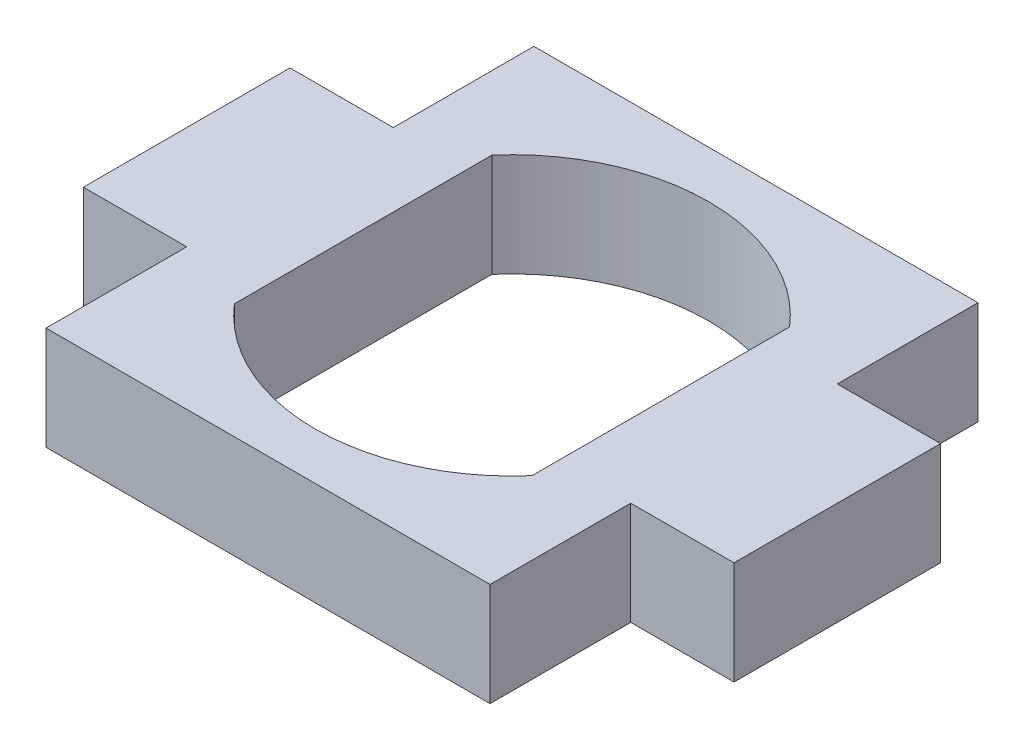
SolidWorks part; units mm, degrees
material "Acrylic (Medium-high impact)"
ref_plane "Front Plane" through (0, 0, 0) normal (0, 0, 1) x (1, 0, 0)
ref_plane "Top Plane" through (0, 0, 0) normal (0, 1, 0) x (1, 0, 0)
ref_plane "Right Plane" through (0, 0, 0) normal (1, 0, 0) x (0, 0, -1)
sketch "Sketch1" plane through (0, 0, 0) normal (0, 1, 0) x (1, 0, 0)
  line L1 (-13.65, -15) -> (13.65, -15)
  line L2 (-13.65, -15) -> (-13.65, 15)
  line L3 (-13.65, 15) -> (13.65, 15)
  line L4 (13.65, -15) -> (13.65, 15)
  line L5 (-13.65, -15) -> (13.65, 15) construction
  line L6 (-13.65, 15) -> (13.65, -15) construction
  point P0 (0, 0)
  dimension "D1" = 30
  dimension "D2" = 27.3
extrude "Boss-Extrude1" add sketch "Sketch1" along normal blind 6.35
sketch "Sketch2" plane through (13.65, 0, 0) normal (1, 0, 0) x (0, 0, -1)
  line L0 (15, 6.35) -> (-15, 6.35) construction
  line L1 (6.35, 0) -> (-6.35, 0)
  line L2 (6.35, 0) -> (6.35, 6.35)
  line L3 (6.35, 6.35) -> (-6.35, 6.35)
  line L4 (-6.35, 0) -> (-6.35, 6.35)
  line L5 (6.35, 0) -> (-6.35, 6.35) construction
  line L6 (6.35, 6.35) -> (-6.35, 0) construction
  line L7 (15, 0) -> (-15, 0) construction
  line L8 (15, 6.35) -> (15, 0) construction
  point P0 (0, 3.175)
  dimension "D1" = 0
  dimension "D2" = 0
  dimension "D3" = 12.7
  dimension "D4" = 15
extrude "Boss-Extrude2" add sketch "Sketch2" along normal blind 6.35
mirror "Mirror1" about plane through (0, 0, 0) normal (1, 0, 0) of "Boss-Extrude2"
sketch "Sketch3" plane through (0, 6.35, 0) normal (0, 1, 0) x (1, 0, 0)
  line L2 (-9.15, -7.9175) -> (-9.15, 7.9175)
  line L4 (9.15, -7.9175) -> (9.15, 7.9175)
  line L5 (-9.15, -7.9175) -> (9.15, 7.9175) construction
  line L6 (-9.15, 7.9175) -> (9.15, -7.9175) construction
  arc A0 (-9.15, -7.9175) -> (9.15, -7.9175) centre (0, 0) ccw
  arc A1 (9.15, 7.9175) -> (-9.15, 7.9175) centre (0, 0) ccw
  dimension "D1" = 24.2
  dimension "D2" = 18.3
extrude "Cut-Extrude1" cut sketch "Sketch3" against normal through all
